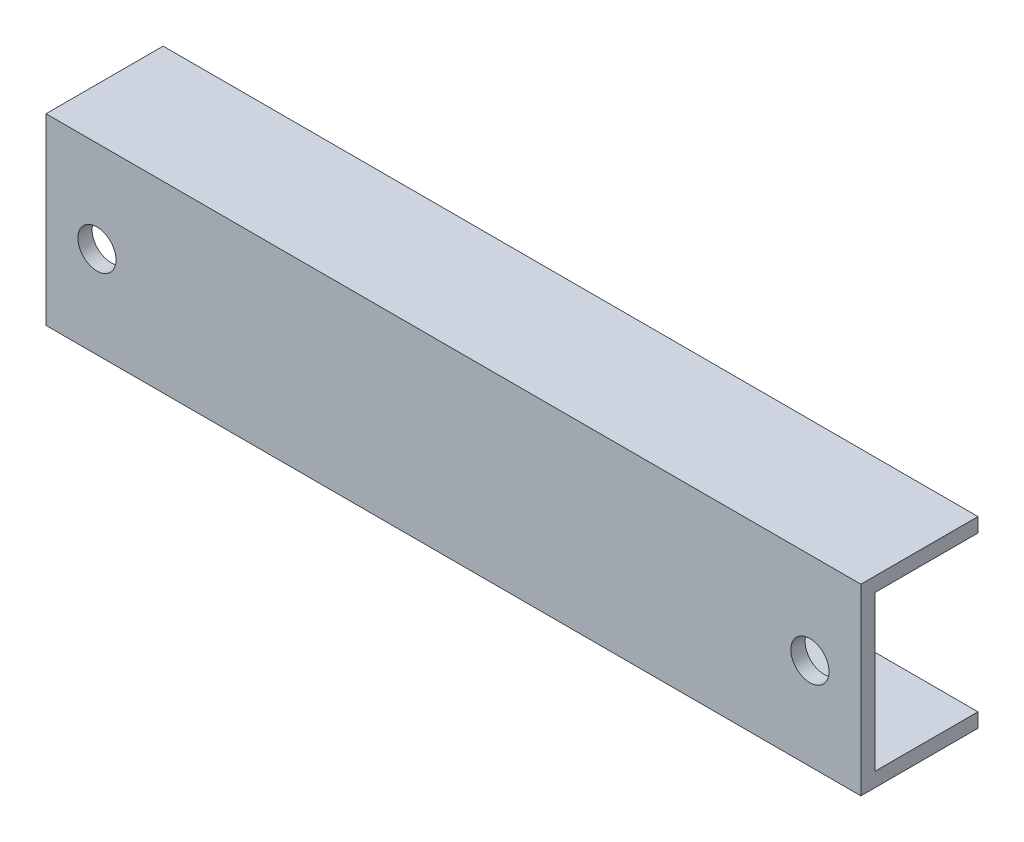
SolidWorks part; units mm, degrees
ref_plane "Front Plane" through (0, 0, 0) normal (0, 0, 1) x (1, 0, 0)
ref_plane "Top Plane" through (0, 0, 0) normal (0, 1, 0) x (1, 0, 0)
ref_plane "Right Plane" through (0, 0, 0) normal (1, 0, 0) x (0, 0, -1)
sketch "Sketch1" plane through (0, 0, 0) normal (1, 0, 0) x (0, 0, -1)
  line L0 (0, 11.43) -> (0, -11.43)
  line L1 (0, -11.43) -> (14.605, -11.43)
  line L2 (14.605, -11.43) -> (14.605, -9.652)
  line L3 (14.605, -9.652) -> (1.778, -9.652)
  line L4 (1.778, -9.652) -> (1.778, 9.652)
  line L5 (1.778, 9.652) -> (14.605, 9.652)
  line L6 (14.605, 9.652) -> (14.605, 11.43)
  line L7 (14.605, 11.43) -> (0, 11.43)
  line L8 (0, 0) -> (4.8403, 0) construction
  dimension "D1" = 14.605
  dimension "D2" = 22.86
  dimension "D3" = 1.778
  dimension "D4" = 19.304
extrude "Boss-Extrude1" add sketch "Sketch1" along normal mid plane 101.6
sketch "Sketch2" plane through (50.8, 0, 0) normal (1, 0, 0) x (0, 0, -1)
  line L0 (0, 0) -> (1.778, 0)
  line L1 (1.778, -9.652) -> (1.778, 9.652) construction
sketch "Sketch3" plane through (0, 0, 0) normal (0, 0, 1) x (1, 0, 0)
  line L0 (38.1, 0) -> (50.8, 0) construction
  line L1 (38.1, 77.216) -> (38.1, -77.216) construction
  line L2 (50.8, -77.216) -> (50.8, 77.216) construction
  circle A0 centre (44.45, 0) radius 2.3812
  dimension "D1" = 4.7625
extrude "Cut-Extrude1" cut sketch "Sketch3" against normal through all
mirror "Mirror1" about plane through (0, 0, 0) normal (1, 0, 0) of "Cut-Extrude1"
